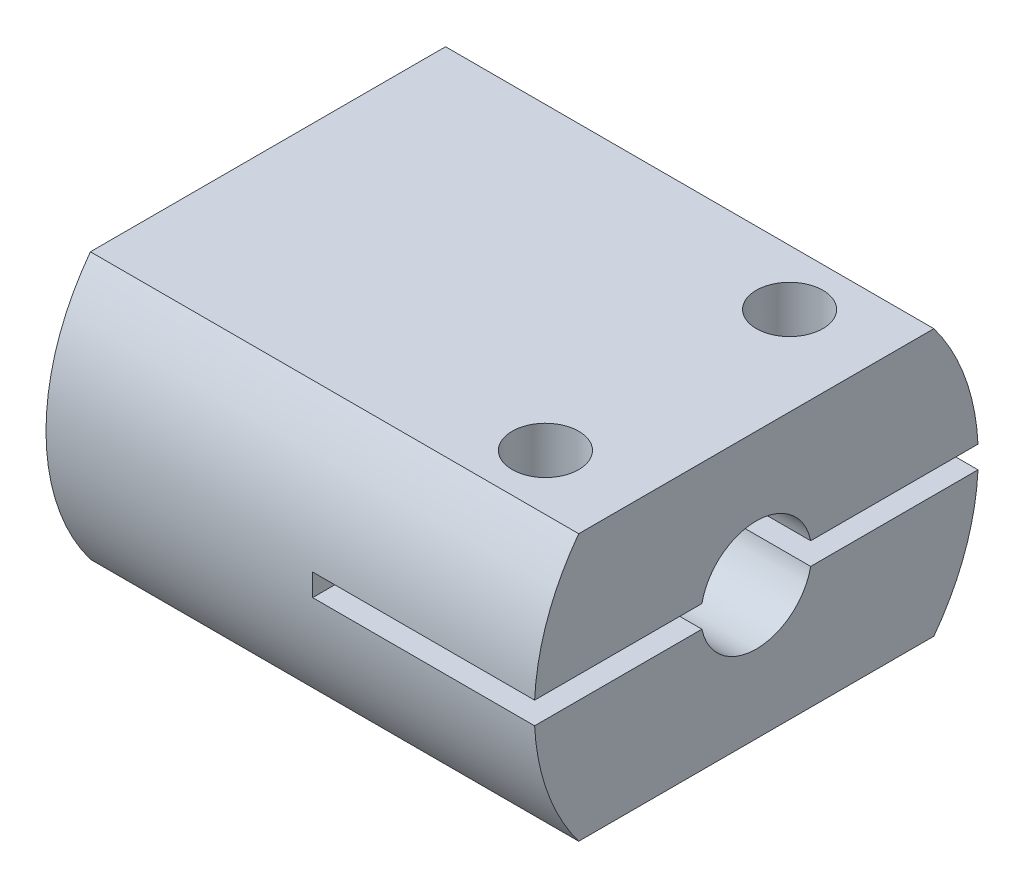
SolidWorks part; units mm, degrees
ref_plane "Front Plane" through (0, 0, 0) normal (0, 0, 1) x (1, 0, 0)
ref_plane "Top Plane" through (0, 0, 0) normal (0, 1, 0) x (1, 0, 0)
ref_plane "Right Plane" through (0, 0, 0) normal (1, 0, 0) x (0, 0, -1)
sketch "Sketch1" plane through (0, 0, 0) normal (1, 0, 0) x (0, 0, -1)
  circle A0 centre (0, 0) radius 10
  dimension "D1" = 20
extrude "Boss-Extrude1" add sketch "Sketch1" along normal blind 22
sketch "Sketch2" plane through (0, 0, 0) normal (-1, 0, 0) x (0, 0, 1)
  line L0 (-2, 3.4641) -> (2, 3.4641)
  arc A0 (-2, 3.4641) -> (2, 3.4641) centre (0, 0) ccw
  dimension "D1" = 8
  dimension "D2" = 4
extrude "Cut-Extrude1" cut sketch "Sketch2" against normal blind 12
sketch "Sketch3" plane through (22, 0, 0) normal (1, 0, 0) x (0, 0, -1)
  line L9 (-10, 0.5) -> (10, 0.5)
  line L10 (-10, 0.5) -> (-10, -0.5)
  line L11 (-10, -0.5) -> (10, -0.5)
  line L12 (10, 0.5) -> (10, -0.5)
  circle A0 centre (0, 0) radius 2.5
  circle A2 centre (0, 0) radius 10 construction
  circle M2 centre (0, 0) radius 10
  dimension "D1" = 5
  dimension "D4" = 0.5
  dimension "D5" = 0.5
extrude "Cut-Extrude2" cut sketch "Sketch3" against normal blind 10 contours A0 L9 L11 M2 | L11 A0 | L9 A0 L11 | L9 A0 | A0 L11 L9 M2
sketch "Sketch5" plane through (22, 0, 0) normal (1, 0, 0) x (0, 0, -1)
  line L1 (-8, 6) -> (8, 6)
  line L2 (-8, 6) -> (-8, 10)
  line L3 (-8, 10) -> (8, 10)
  line L4 (8, 6) -> (8, 10)
  line L5 (8, -6) -> (-8, -6)
  line L6 (8, -6) -> (8, -10)
  line L7 (8, -10) -> (-8, -10)
  line L8 (-8, -6) -> (-8, -10)
  arc A0 (9.9875, 0.5) -> (-9.9875, 0.5) centre (0, 0) ccw construction
  arc A1 (-9.9875, -0.5) -> (9.9875, -0.5) centre (0, 0) ccw construction
  arc A2 (-2.4495, -0.5) -> (2.4495, -0.5) centre (0, 0) ccw construction
  arc A3 (2.4495, 0.5) -> (-2.4495, 0.5) centre (0, 0) ccw construction
  dimension "D1" = 6
  dimension "D2" = 6
extrude "Cut-Extrude4" cut sketch "Sketch5" against normal through all
sketch "Sketch4" plane through (0, 6, 0) normal (0, 1, 0) x (1, 0, 0)
  line L0 (22, 5.5) -> (0, 5.5) construction
  line L3 (0, -5.5) -> (22, -5.5) construction
  line L8 (22, -8) -> (22, 8) construction
  line L9 (0, -8) -> (22, -8) construction
  line L10 (0, 8) -> (22, 8) construction
  line L11 (0, -8) -> (0, 8) construction
  circle A0 centre (18, 5.5) radius 1.5
  circle A1 centre (18, -5.5) radius 1.5
  dimension "D3" = 3
  dimension "D4" = 3
  dimension "D5" = 4
  dimension "D6" = 2.5
  dimension "D2" = 4
  dimension "D1" = 2.5
extrude "Cut-Extrude3" cut sketch "Sketch4" against normal through all
